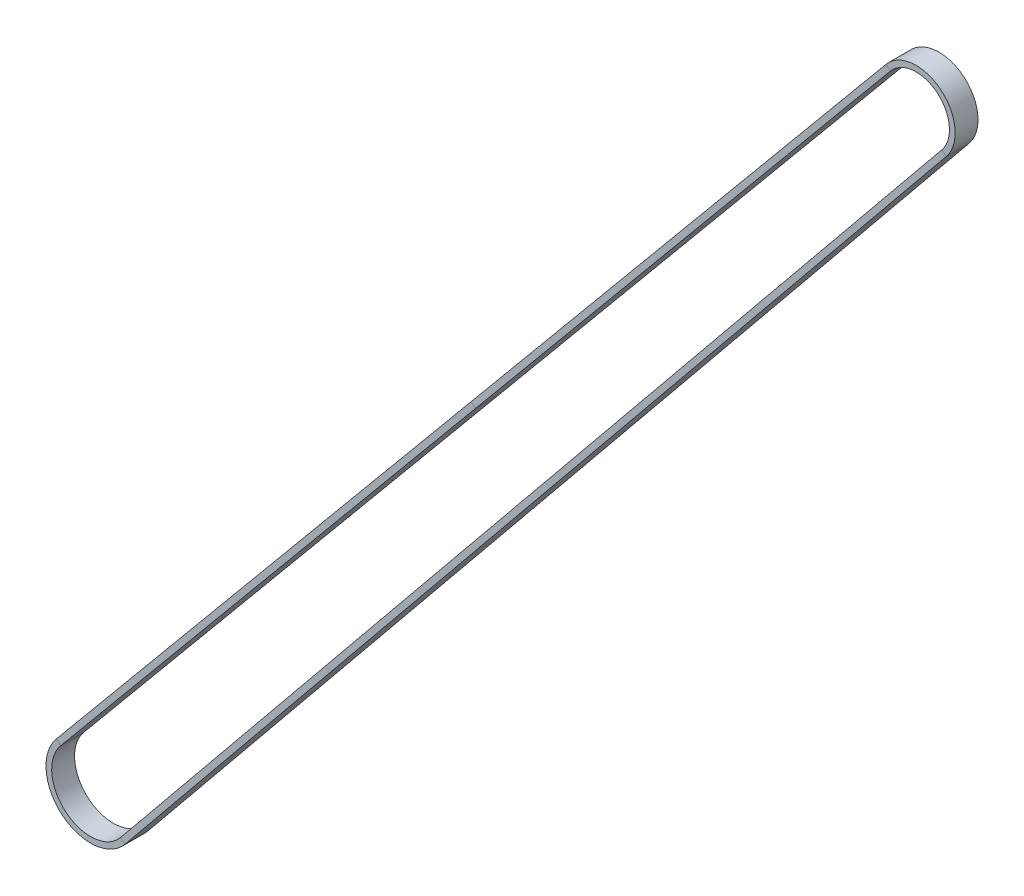
SolidWorks part; units mm, degrees
material "POLYURETHANE (11671)"
ref_plane "Front Plane" through (0, 0, 0) normal (0, 0, 1) x (1, 0, 0)
ref_plane "Top Plane" through (0, 0, 0) normal (0, 1, 0) x (1, 0, 0)
ref_plane "Right Plane" through (0, 0, 0) normal (1, 0, 0) x (0, 0, -1)
sketch "Sketch1" plane through (0, 0, 0) normal (0, 0, 1) x (1, 0, 0)
  line L0 (209.9427, 268.777) -> (-7.847, 6.5164)
  line L1 (7.9022, -6.4494) -> (223.453, 257.6543)
  circle A0 centre (0, 0) radius 10.2 construction
  arc A1 (-7.847, 6.5164) -> (7.9022, -6.4494) centre (0, 0) ccw
  circle A2 centre (216.6742, 263.1869) radius 8.75 construction
  arc A3 (223.453, 257.6543) -> (209.9427, 268.777) centre (216.6742, 263.1869) ccw
  point P2 (101.0478, 137.6467)
ref_plane "Plane1" through (101.0478, 137.6467, 0) normal (-0.6389, -0.7693, 0) x (-0.7693, 0.6389, 0)
sketch "Sketch2" plane through (101.0478, 137.6467, 0) normal (-0.6389, -0.7693, 0) x (-0.7693, 0.6389, 0)
  line L1 (1.5, -3) -> (0, -3)
  line L2 (1.5, -3) -> (1.5, 3)
  line L3 (1.5, 3) -> (0, 3)
  line L4 (0, -3) -> (0, 3)
  point P4 (0, 0)
  dimension "D1" = 1.5
  dimension "D2" = 6
sweep "Sweep1" add profiles "Sketch2" path "Sketch1"
ref_plane "Plane2" through (0, 0, 0) normal (0, 0, 1) x (1, 0, 0)
